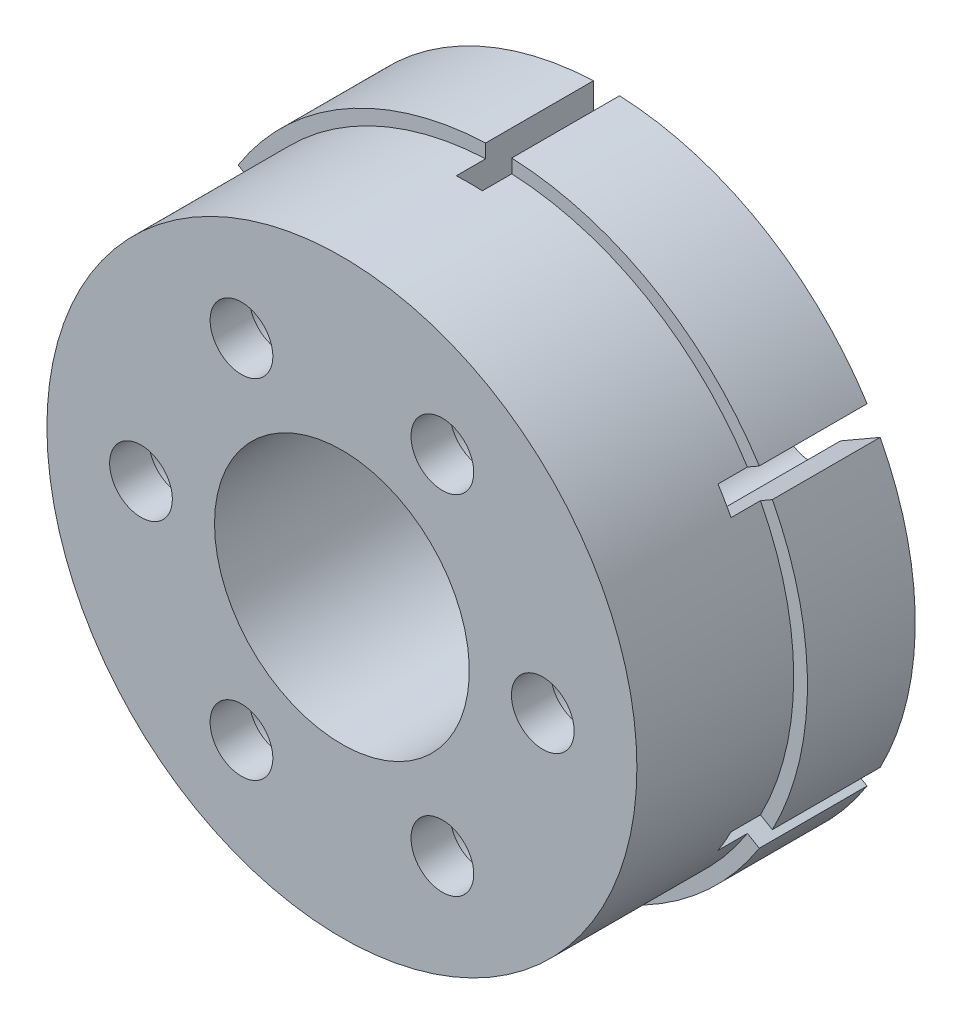
SolidWorks part; units mm, degrees
ref_plane "前视基准面" through (0, 0, 0) normal (0, 0, 1) x (1, 0, 0)
ref_plane "上视基准面" through (0, 0, 0) normal (0, 1, 0) x (1, 0, 0)
ref_plane "右视基准面" through (0, 0, 0) normal (1, 0, 0) x (0, 0, -1)
sketch "草图1" plane through (0, 0, 0) normal (0, 0, 1) x (1, 0, 0)
  circle A0 centre (0, 0) radius 15.75
  dimension "D1" = 31.5
extrude "凸台-拉伸1" add sketch "草图1" along normal blind 5.5
sketch "草图3" plane through (0, 0, 5.5) normal (0, 0, 1) x (1, 0, 0)
  circle A0 centre (0, 0) radius 15.05
  dimension "D1" = 30.1
extrude "凸台-拉伸2" add sketch "草图3" along normal blind 8
sketch "草图4" plane through (0, 0, 0) normal (0, 0, -1) x (-1, 0, 0)
  line L0 (-10.25, 0) -> (0, 0) construction
  circle A0 centre (-10.25, 0) radius 1.6
  dimension "D2" = 3.2
  dimension "D1" = 10.25
extrude "切除-拉伸2" cut sketch "草图4" against normal through all
sketch "草图5" plane through (0, 0, 0) normal (0, 0, -1) x (-1, 0, 0)
  circle A0 centre (-10.25, 0) radius 2.15
  dimension "D1" = 4.3
extrude "切除-拉伸3" cut sketch "草图5" against normal offset from surface (11.5 mm away) 2 up to face at (8.65, 0, 13.5)
sketch "草图8" plane through (0, 0, 0) normal (0, 0, -1) x (-1, 0, 0)
  circle A0 centre (-10.25, 0) radius 3.5
  dimension "D1" = 7
extrude "切除-拉伸7" cut sketch "草图8" against normal offset from surface (5.5 mm away) 6 up to face at (12.4, 0, 11.5)
pattern_circular "阵列(圆周)2" count 6 over 360 about axis through (0, 0, 0) along (0, 0, 1) of "切除-拉伸2", "切除-拉伸3", "切除-拉伸7"
sketch "草图2" plane through (0, 0, 0) normal (0, 0, -1) x (-1, 0, 0)
  line L0 (0, 12) -> (0, 0) construction
  circle A0 centre (0, 12) radius 1.55
  dimension "D2" = 3.1
  dimension "D1" = 12
sketch "草图6" plane through (0, 0, 0) normal (0, 0, -1) x (-1, 0, 0)
  circle A0 centre (0, 0) radius 6.5
  dimension "D1" = 13
extrude "切除-拉伸4" cut sketch "草图6" against normal through all
sketch "草图7" plane through (0, 0, 0) normal (0, 0, -1) x (-1, 0, 0)
  circle A0 centre (0, 0) radius 7.55
  dimension "D1" = 15.1
extrude "切除-拉伸5" cut sketch "草图7" against normal blind 4
extrude "切除-拉伸6" cut sketch "草图2" against normal blind 7
sketch "草图9" plane through (0, 0, 0) normal (0, 0, -1) x (-1, 0, 0)
  line L1 (-0.6652, 16.4) -> (0.6652, 16.4)
  line L2 (-0.6652, 16.4) -> (-0.6652, 13.4)
  line L3 (-0.6652, 13.4) -> (0.6652, 13.4)
  line L4 (0.6652, 16.4) -> (0.6652, 13.4)
  line L5 (0, 13.4) -> (0, 16.4) construction
  line L6 (-0.6652, 14.9) -> (0.6652, 14.9) construction
  circle A0 centre (0, 12) radius 1.55 construction
  circle A1 centre (0, 12) radius 1.55 construction
  circle A2 centre (0, 12) radius 1.55 construction
  point P0 (0, 14.9)
  dimension "D1" = 1.4
  dimension "D2" = 3
extrude "切除-拉伸8" cut sketch "草图9" against normal up to surface (7 mm away) up to face at (-1.55, 12, 7)
pattern_circular "阵列(圆周)3" count 6 over 360 about axis through (0, 0, 0) along (0, 0, 1) of "切除-拉伸6", "切除-拉伸8"
